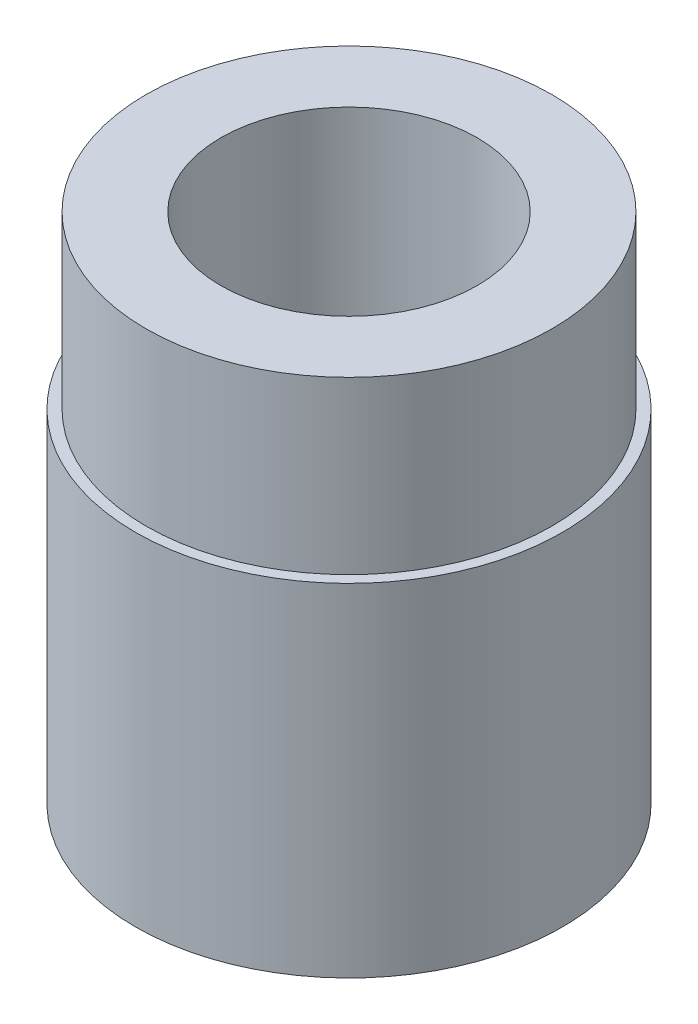
SolidWorks part; units mm, degrees
ref_plane "Front Plane" through (0, 0, 0) normal (0, 0, 1) x (1, 0, 0)
ref_plane "Top Plane" through (0, 0, 0) normal (0, 1, 0) x (1, 0, 0)
ref_plane "Right Plane" through (0, 0, 0) normal (1, 0, 0) x (0, 0, -1)
sketch "Sketch1" plane through (0, 0, 0) normal (0, 1, 0) x (1, 0, 0)
  circle A0 centre (0, 0) radius 31.75
  circle A1 centre (0, 0) radius 19.05
  dimension "D1" = 63.5
  dimension "D2" = 38.1
extrude "Boss-Extrude1" add sketch "Sketch1" along normal blind 76.2
sketch "Sketch3" plane through (0, 76.2, 0) normal (0, 1, 0) x (1, 0, 0)
  circle A0 centre (0, 0) radius 30.1625
  circle A1 centre (0, 0) radius 31.75
  dimension "D1" = 63.5
  dimension "D2" = 60.325
extrude "Cut-Extrude1" cut sketch "Sketch3" against normal blind 25.4
